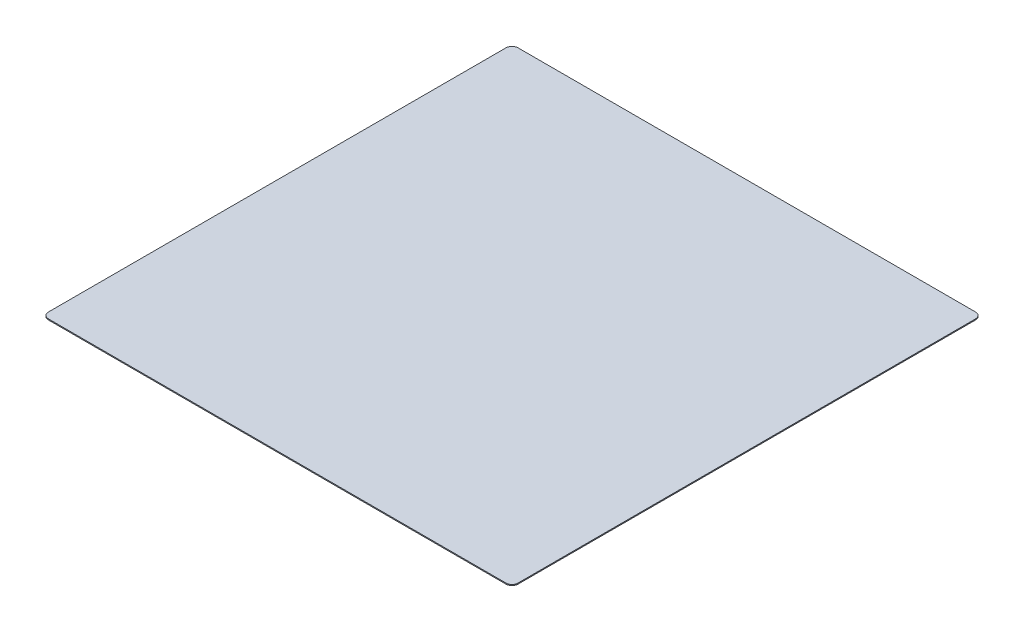
SolidWorks part; units mm, degrees
ref_plane "Ebene vorne" through (0, 0, 0) normal (0, 0, 1) x (1, 0, 0)
ref_plane "Ebene oben" through (0, 0, 0) normal (0, 1, 0) x (1, 0, 0)
ref_plane "Ebene rechts" through (0, 0, 0) normal (1, 0, 0) x (0, 0, -1)
sketch "Skizze1" plane through (0, 0, 0) normal (0, 1, 0) x (1, 0, 0)
  line L0 (-114.5, -117.5) -> (114.5, -117.5)
  line L1 (117.5, -114.5) -> (117.5, 114.5)
  line L2 (114.5, 117.5) -> (-114.5, 117.5)
  line L3 (-117.5, 114.5) -> (-117.5, -114.5)
  line L4 (0, 117.5) -> (0, -117.5) construction
  line L5 (-117.5, 0) -> (117.5, 0) construction
  arc A0 (-117.5, -114.5) -> (-114.5, -117.5) centre (-114.5, -114.5) ccw
  arc A1 (114.5, -117.5) -> (117.5, -114.5) centre (114.5, -114.5) ccw
  arc A2 (117.5, 114.5) -> (114.5, 117.5) centre (114.5, 114.5) ccw
  arc A3 (-114.5, 117.5) -> (-117.5, 114.5) centre (-114.5, 114.5) ccw
  dimension "D2" = 3
  dimension "D1" = 235
extrude "Aufsatz-Linear austragen1" add sketch "Skizze1" along normal blind 0.5
